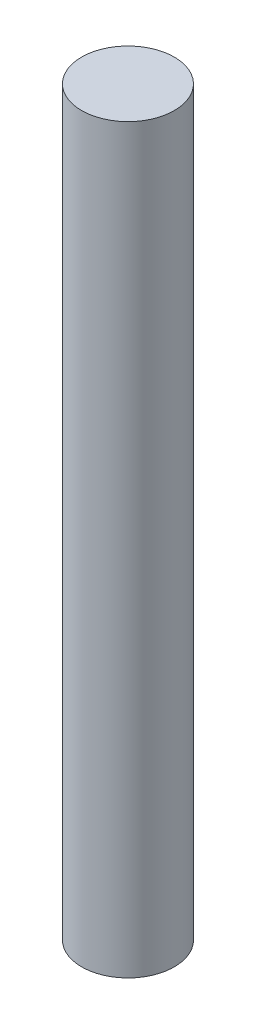
SolidWorks part; units mm, degrees
material "1060 Alloy"
ref_plane "Front Plane" through (0, 0, 0) normal (0, 0, 1) x (1, 0, 0)
ref_plane "Top Plane" through (0, 0, 0) normal (0, 1, 0) x (1, 0, 0)
ref_plane "Right Plane" through (0, 0, 0) normal (1, 0, 0) x (0, 0, -1)
sketch "Sketch1" plane through (0, 0, 0) normal (0, 0, 1) x (1, 0, 0)
  line L0 (0, 101.6) -> (0, -101.6) construction
  line L1 (0, 76.2) -> (9.525, 76.2)
  line L2 (9.525, 76.2) -> (9.525, -76.2)
  line L3 (9.525, -76.2) -> (0, -76.2)
  line L4 (0, 76.2) -> (0, -76.2)
  point P5 (9.525, 0)
  dimension "D1" = 152.4
  dimension "D2" = 19.05
revolve "Revolve1" add sketch "Sketch1" angle 360 about L0
ref_point "Point2"
ref_point "Point4"
equation "\"Rod Diameter\"= 0.75in'This will remain constant in the steering column"
equation "\"Rod Length\"= 6in'This might change for different rods in steering column"
equation "\"D1@Sketch1\"= \"Rod Length\""
equation "\"D2@Sketch1\"=\"Rod Diameter\""
